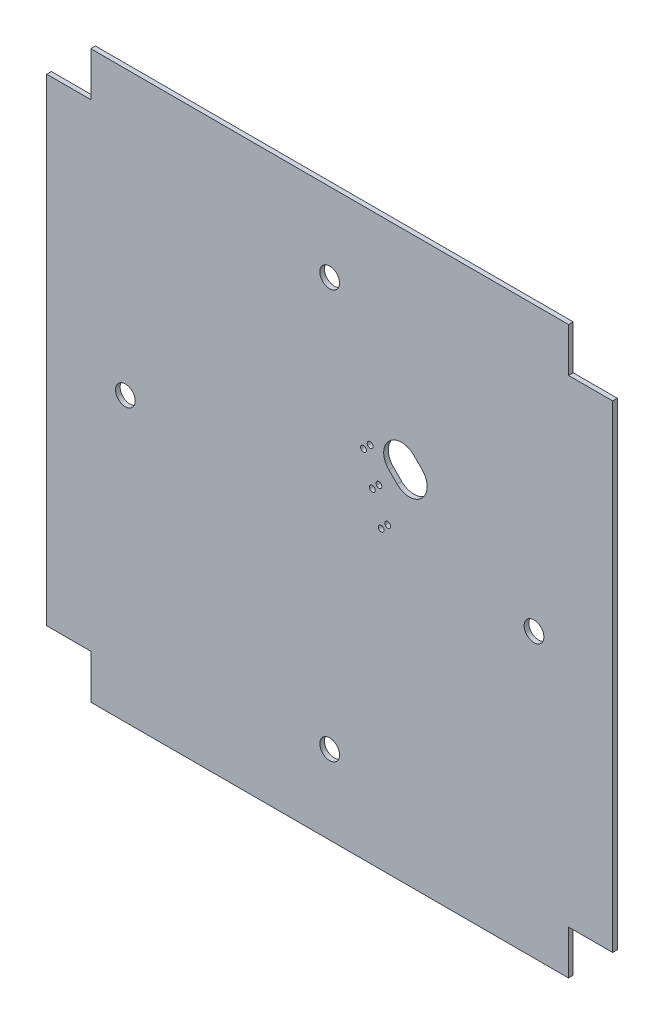
SolidWorks part; units mm, degrees
ref_plane "Front Plane" through (0, 0, 0) normal (0, 0, 1) x (1, 0, 0)
ref_plane "Top Plane" through (0, 0, 0) normal (0, 1, 0) x (1, 0, 0)
ref_plane "Right Plane" through (0, 0, 0) normal (1, 0, 0) x (0, 0, -1)
sketch "Sketch1" plane through (0, 0, 0) normal (0, 0, 1) x (1, 0, 0)
  line L52 (48.75, -48.75) -> (-48.75, -48.75)
  line L53 (48.75, -48.75) -> (48.75, 48.75)
  line L54 (48.75, 48.75) -> (-48.75, 48.75)
  line L55 (-48.75, -48.75) -> (-48.75, 48.75)
  line L56 (48.75, -48.75) -> (-48.75, 48.75) construction
  line L57 (48.75, 48.75) -> (-48.75, -48.75) construction
  point P0 (0, 0)
  dimension "D1" = 97.5
  dimension "D2" = 97.5
extrude "Boss-Extrude1" add sketch "Sketch1" along normal blind 0.8
sketch "Sketch2" plane through (0, 0, 0) normal (0, 0, -1) x (-1, 0, 0)
  line L1 (-48.75, 48.75) -> (-41.15, 48.75)
  line L2 (-48.75, 48.75) -> (-48.75, 41.15)
  line L3 (-48.75, 41.15) -> (-41.15, 41.15)
  line L4 (48.75, 48.75) -> (-48.75, 48.75)
  line L5 (-48.75, 48.75) -> (-48.75, -48.75)
  line L6 (-48.75, -48.75) -> (48.75, -48.75)
  line L7 (48.75, -48.75) -> (48.75, 48.75)
  line L8 (48.75, 48.75) -> (-48.75, 48.75) construction
  line L9 (-48.75, 48.75) -> (-48.75, -48.75) construction
  line L10 (-48.75, -48.75) -> (48.75, -48.75) construction
  line L11 (48.75, -48.75) -> (48.75, 48.75) construction
  line L12 (-41.15, 48.75) -> (-41.15, 41.15)
  line L13 (-48.75, -48.75) -> (-41.15, -48.75)
  line L14 (-48.75, -48.75) -> (-48.75, -41.15)
  line L15 (-48.75, -41.15) -> (-41.15, -41.15)
  line L16 (-41.15, -48.75) -> (-41.15, -41.15)
  line L17 (48.75, -48.75) -> (41.15, -48.75)
  line L18 (48.75, -48.75) -> (48.75, -41.15)
  line L19 (48.75, -41.15) -> (41.15, -41.15)
  line L20 (41.15, -48.75) -> (41.15, -41.15)
  line L21 (48.75, 48.75) -> (41.15, 48.75)
  line L22 (48.75, 48.75) -> (48.75, 41.15)
  line L23 (48.75, 41.15) -> (41.15, 41.15)
  line L24 (41.15, 48.75) -> (41.15, 41.15)
  dimension "D2" = 7.6
  dimension "D3" = 7.6
  dimension "D4" = 7.6
  dimension "D5" = 7.6
  dimension "D6" = 7.6
  dimension "D7" = 7.6
  dimension "D8" = 7.6
  dimension "D9" = 7.6
  dimension "D1" = 0
extrude "Cut-Extrude1" cut sketch "Sketch2" against normal through all
sketch "Sketch3" plane through (0, 0, 0) normal (0, 0, -1) x (-1, 0, 0)
  line L0 (0, 0) -> (0, 48.75) construction
  line L1 (-41.15, 48.75) -> (41.15, 48.75) construction
  line L2 (48.75, 0) -> (0, 0) construction
  line L3 (48.75, -41.15) -> (48.75, 41.15) construction
  line L4 (0, 0) -> (0, -48.75) construction
  line L5 (-41.15, -48.75) -> (41.15, -48.75) construction
  line L6 (0, 0) -> (-48.75, 0) construction
  line L7 (-48.75, -41.15) -> (-48.75, 41.15) construction
  circle A4 centre (0, 35.2) radius 1.7
  circle A5 centre (35.2, 0) radius 1.7
  circle A6 centre (0, -35.2) radius 1.7
  circle A7 centre (-35.2, 0) radius 1.7
  dimension "D5" = 3.4
  dimension "D6" = 3.4
  dimension "D7" = 3.4
  dimension "D8" = 3.4
  dimension "D1" = 35.2
  dimension "D2" = 35.2
  dimension "D3" = 35.2
  dimension "D4" = 35.2
extrude "Cut-Extrude2" cut sketch "Sketch3" against normal through all
sketch "Sketch4" plane through (0, 0, 0) normal (0, 0, -1) x (-1, 0, 0)
  line L5 (-18.0312, 12.3744) -> (-13.7179, 8.061)
  line L6 (-18.0312, 12.3744) -> (-12.3744, 18.0312)
  line L7 (-13.7179, 8.061) -> (-8.061, 13.7179)
  line L8 (-12.3744, 18.0312) -> (-8.061, 13.7179)
  line L9 (-41.15, -48.75) -> (41.15, -48.75) construction
  point P7 (-10.8894, 10.8894)
  point P8 (-132.2984, 65.8162)
  dimension "D1" = 45
  dimension "D2" = 15.4
  dimension "D3" = 6.1
  dimension "D4" = 8
  dimension "D5" = 15.4
extrude "Cut-Extrude3" cut sketch "Sketch4" against normal through all
sketch "Sketch5" plane through (0, 0, 0) normal (0, 0, -1) x (-1, 0, 0)
  line L0 (-13.6445, 20.362) -> (1.9772, 4.7403) construction
  line L1 (6.4476, -6.4476) -> (-13.8137, 13.8137) construction
  line L3 (-27.4578, 20.7403) -> (-3.487, -3.2305) construction
  line L7 (-8.061, 13.7179) -> (-12.3744, 18.0312) construction
  line L8 (-13.7179, 8.061) -> (-8.061, 13.7179) construction
  line L9 (-13.7179, 8.061) -> (-8.061, 13.7179) construction
  circle A6 centre (-6.965, 13.6825) radius 0.5
  circle A7 centre (-5.8336, 12.5511) radius 0.5
  circle A9 centre (-8.4853, 8.4853) radius 0.5
  circle A10 centre (-7.3539, 7.3539) radius 0.5
  circle A12 centre (-10.0056, 3.288) radius 0.5
  circle A13 centre (-8.8742, 2.1567) radius 0.5
  dimension "D2" = 1
  dimension "D3" = 1
  dimension "D4" = 4.75
  dimension "D5" = 1
  dimension "D6" = 1
  dimension "D8" = 4.75
  dimension "D9" = 1
  dimension "D14" = 1
  dimension "D7" = 0.75
  dimension "D10" = 1.6
  dimension "D11" = 3.4
  dimension "D12" = 0.8
  dimension "D13" = 1.6
  dimension "D15" = 6
  dimension "D16" = 1.6
extrude "Cut-Extrude4" cut sketch "Sketch5" against normal through all
fillet "Fillet2" radius 3 4 edges at (8.061, 13.7179, 0.4) (13.7179, 8.061, 0.4) (18.0312, 12.3744, 0.4) (12.3744, 18.0312, 0.4)
